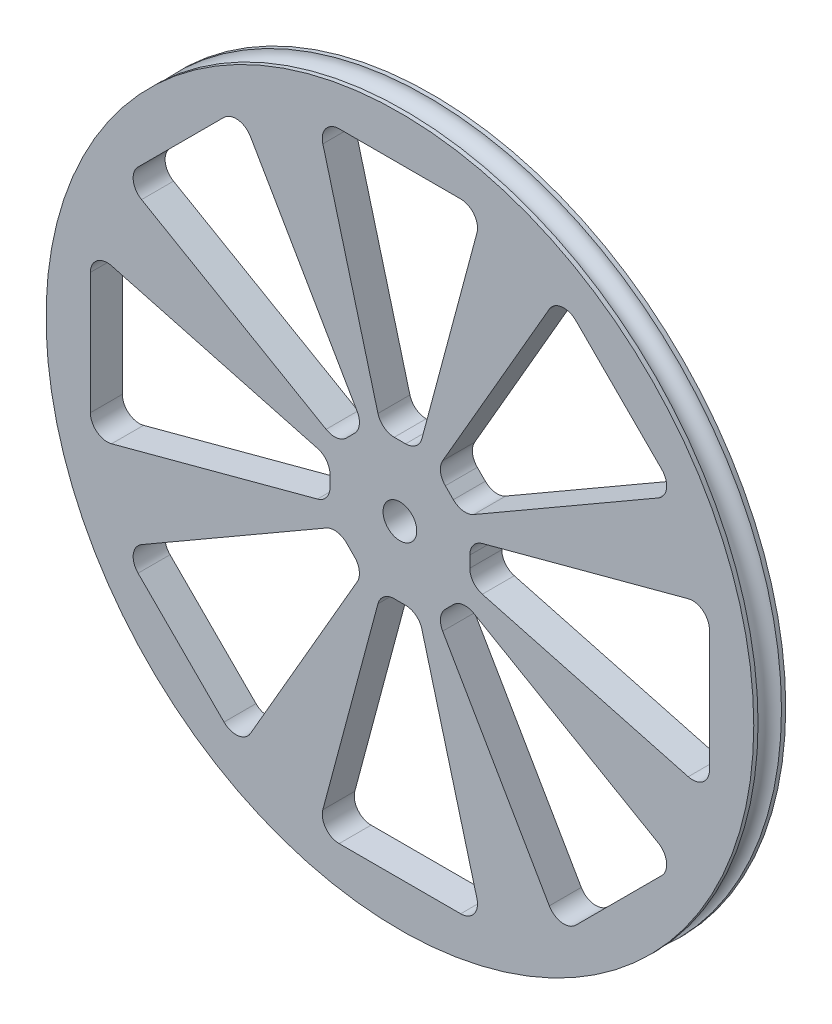
SolidWorks part; units mm, degrees
ref_plane "Front Plane" through (0, 0, 0) normal (0, 0, 1) x (1, 0, 0)
ref_plane "Top Plane" through (0, 0, 0) normal (0, 1, 0) x (1, 0, 0)
ref_plane "Right Plane" through (0, 0, 0) normal (1, 0, 0) x (0, 0, -1)
sketch "Sketch1" plane through (0, 0, 0) normal (1, 0, 0) x (0, 0, -1)
  line L0 (-2.4096, -44.4892) -> (-2.4096, 6.3108)
  line L1 (-2.4096, 6.3108) -> (-1.7653, 6.3108)
  line L4 (-2.4096, -44.4892) -> (2.4096, -44.4892)
  line L5 (-19.2512, -47.0292) -> (14.1572, -47.0292) construction
  line L7 (0, -2.77) -> (0, 6.9) construction
  line L8 (2.4096, -44.4892) -> (2.4096, 6.3108)
  line L9 (2.4096, 6.3108) -> (1.7653, 6.3108)
  arc A1 (-1.7653, 6.3108) -> (1.7653, 6.3108) centre (0, 6.3108) ccw
  point P12 (0, 0)
  dimension "D2" = 2.54
  dimension "D1" = 1.7653
  dimension "D3" = 53.34
revolve "Revolve1" add sketch "Sketch1" angle 360 about L5
sketch "Sketch2" plane through (0, 0, -2.4096) normal (0, 0, -1) x (-1, 0, 0)
  line L0 (0, -126.2324) -> (0, 33.6703) construction
  line L1 (-65.9362, -47.0292) -> (81.1983, -47.0292) construction
  line L2 (-9.1616, -0.3735) -> (9.1616, -0.3735)
  line L3 (11.6152, -3.57) -> (3.3104, -34.6075)
  line L4 (0.8568, -36.4909) -> (-0.8568, -36.4909)
  line L5 (-11.6152, -3.57) -> (-3.3104, -34.6075)
  line L6 (38.9435, -24.5121) -> (11.1243, -40.5866)
  line L7 (26.5124, -7.5604) -> (39.4688, -20.5168)
  line L8 (22.5171, -8.0857) -> (6.4426, -35.9049)
  line L9 (8.0575, -40.1833) -> (6.8459, -38.9717)
  line L10 (43.4592, -58.6444) -> (12.4217, -50.3396)
  line L11 (46.6557, -37.8676) -> (46.6557, -56.1908)
  line L12 (43.4592, -35.414) -> (12.4217, -43.7188)
  line L13 (10.5383, -47.8859) -> (10.5383, -46.1724)
  line L14 (22.5171, -85.9727) -> (6.4426, -58.1535)
  line L15 (39.4688, -73.5416) -> (26.5124, -86.498)
  line L16 (38.9435, -69.5463) -> (11.1243, -53.4718)
  line L17 (6.8459, -55.0867) -> (8.0575, -53.8751)
  line L18 (-11.6152, -90.4884) -> (-3.3104, -59.4509)
  line L19 (9.1616, -93.6849) -> (-9.1616, -93.6849)
  line L20 (11.6152, -90.4884) -> (3.3104, -59.4509)
  line L21 (-0.8568, -57.5674) -> (0.8568, -57.5674)
  line L22 (-38.9435, -69.5463) -> (-11.1243, -53.4718)
  line L23 (-26.5124, -86.498) -> (-39.4688, -73.5416)
  line L24 (-22.5171, -85.9727) -> (-6.4426, -58.1535)
  line L25 (-8.0575, -53.8751) -> (-6.8459, -55.0867)
  line L26 (-43.4592, -35.414) -> (-12.4217, -43.7188)
  line L27 (-46.6557, -56.1908) -> (-46.6557, -37.8676)
  line L28 (-43.4592, -58.6444) -> (-12.4217, -50.3396)
  line L29 (-10.5383, -46.1724) -> (-10.5383, -47.8859)
  line L30 (-22.5171, -8.0857) -> (-6.4426, -35.9049)
  line L31 (-39.4688, -20.5168) -> (-26.5124, -7.5604)
  line L32 (-38.9435, -24.5121) -> (-11.1243, -40.5866)
  line L33 (-6.8459, -38.9717) -> (-8.0575, -40.1833)
  arc A0 (11.6152, -3.57) -> (9.1616, -0.3735) centre (9.1616, -2.9135) ccw
  arc A1 (3.3104, -34.6075) -> (0.8568, -36.4909) centre (0.8568, -33.9509) cw
  arc A2 (-3.3104, -34.6075) -> (-0.8568, -36.4909) centre (-0.8568, -33.9509) ccw
  arc A3 (-11.6152, -3.57) -> (-9.1616, -0.3735) centre (-9.1616, -2.9135) cw
  arc A4 (38.9435, -24.5121) -> (39.4688, -20.5168) centre (37.6727, -22.3129) ccw
  arc A5 (22.5171, -8.0857) -> (26.5124, -7.5604) centre (24.7163, -9.3565) cw
  arc A6 (6.4426, -35.9049) -> (6.8459, -38.9717) centre (8.6419, -37.1757) ccw
  arc A7 (11.1243, -40.5866) -> (8.0575, -40.1833) centre (9.8535, -38.3873) cw
  arc A8 (43.4592, -58.6444) -> (46.6557, -56.1908) centre (44.1157, -56.1908) ccw
  arc A9 (43.4592, -35.414) -> (46.6557, -37.8676) centre (44.1157, -37.8676) cw
  arc A10 (12.4217, -43.7188) -> (10.5383, -46.1724) centre (13.0783, -46.1724) ccw
  arc A11 (12.4217, -50.3396) -> (10.5383, -47.8859) centre (13.0783, -47.8859) cw
  arc A12 (22.5171, -85.9727) -> (26.5124, -86.498) centre (24.7163, -84.7019) ccw
  arc A13 (38.9435, -69.5463) -> (39.4688, -73.5416) centre (37.6727, -71.7455) cw
  arc A14 (11.1243, -53.4718) -> (8.0575, -53.8751) centre (9.8535, -55.6711) ccw
  arc A15 (6.4426, -58.1535) -> (6.8459, -55.0867) centre (8.6419, -56.8827) cw
  arc A16 (-11.6152, -90.4884) -> (-9.1616, -93.6849) centre (-9.1616, -91.1449) ccw
  arc A17 (11.6152, -90.4884) -> (9.1616, -93.6849) centre (9.1616, -91.1449) cw
  arc A18 (3.3104, -59.4509) -> (0.8568, -57.5674) centre (0.8568, -60.1074) ccw
  arc A19 (-3.3104, -59.4509) -> (-0.8568, -57.5674) centre (-0.8568, -60.1074) cw
  arc A20 (-38.9435, -69.5463) -> (-39.4688, -73.5416) centre (-37.6727, -71.7455) ccw
  arc A21 (-22.5171, -85.9727) -> (-26.5124, -86.498) centre (-24.7163, -84.7019) cw
  arc A22 (-6.4426, -58.1535) -> (-6.8459, -55.0867) centre (-8.6419, -56.8827) ccw
  arc A23 (-11.1243, -53.4718) -> (-8.0575, -53.8751) centre (-9.8535, -55.6711) cw
  arc A24 (-43.4592, -35.414) -> (-46.6557, -37.8676) centre (-44.1157, -37.8676) ccw
  arc A25 (-43.4592, -58.6444) -> (-46.6557, -56.1908) centre (-44.1157, -56.1908) cw
  arc A26 (-12.4217, -50.3396) -> (-10.5383, -47.8859) centre (-13.0783, -47.8859) ccw
  arc A27 (-12.4217, -43.7188) -> (-10.5383, -46.1724) centre (-13.0783, -46.1724) cw
  arc A28 (-22.5171, -8.0857) -> (-26.5124, -7.5604) centre (-24.7163, -9.3565) ccw
  arc A29 (-38.9435, -24.5121) -> (-39.4688, -20.5168) centre (-37.6727, -22.3129) cw
  arc A30 (-11.1243, -40.5866) -> (-8.0575, -40.1833) centre (-9.8535, -38.3873) ccw
  arc A31 (-6.4426, -35.9049) -> (-6.8459, -38.9717) centre (-8.6419, -37.1757) cw
  point P15 (0, -0.3735)
  point P18 (0, -36.4909)
  point P107 (0, -47.0292)
  dimension "D1" = 2.54
  dimension "D2" = 2.54
  dimension "D3" = 8
extrude "Cut-Extrude1" cut sketch "Sketch2" against normal blind 7.62
